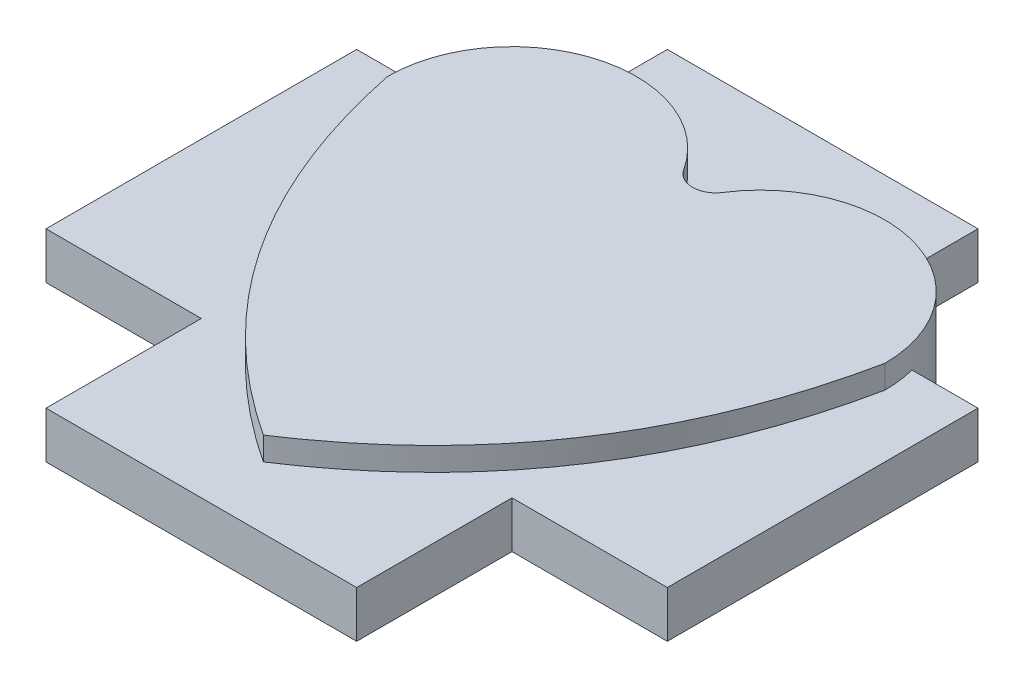
SolidWorks part; units mm, degrees
ref_plane "Front Plane" through (0, 0, 0) normal (0, 0, 1) x (1, 0, 0)
ref_plane "Top Plane" through (0, 0, 0) normal (0, 1, 0) x (1, 0, 0)
ref_plane "Right Plane" through (0, 0, 0) normal (1, 0, 0) x (0, 0, -1)
sketch "Sketch1" plane through (0, 0, 0) normal (0, 1, 0) x (1, 0, 0)
  line L0 (0, 8) -> (0, 4) construction
  line L1 (10, -10) -> (-10, -10)
  line L2 (10, -10) -> (10, 10)
  line L3 (10, 10) -> (-10, 10)
  line L4 (-10, -10) -> (-10, 10)
  line L5 (8, -8) -> (-8, -8) construction
  line L6 (8, -8) -> (8, 8) construction
  line L7 (8, 8) -> (-8, 8) construction
  line L8 (-8, -8) -> (-8, 8) construction
  line L9 (0, 4) -> (4, 4) construction
  line L10 (0, 4) -> (-4, 4) construction
  line L11 (0, -8) -> (0, -4.5) construction
  line L12 (0, -4.5) -> (-4, -4.5) construction
  line L13 (0, -4.5) -> (4, -4.5) construction
  arc A0 (-0.6316, 6.1573) -> (-8, 4) centre (-4, 4) ccw
  arc A1 (8, 4) -> (0.6316, 6.1573) centre (4, 4) ccw
  arc A2 (-0.6316, 6.1573) -> (0.6316, 6.1573) centre (0, 6.5617) ccw
  spline S0 degree 2 poles (-8, 4) (-6.4033, -3.8115) (0, -8) knots 0 0 0 1 1 1
  spline S1 degree 2 poles (8, 4) (6.4033, -3.8115) (0, -8) knots 0 0 0 1 1 1
  point P0 (0, 0)
  point P6 (0, 0)
  dimension "D3" = 0.75
  dimension "D1" = 20
  dimension "D2" = 20
  dimension "D4" = 16
  dimension "D5" = 4
  dimension "D6" = 4
  dimension "D8" = 3.5
  dimension "D9" = 4
  dimension "D10" = 4
extrude "Boss-Extrude3" add sketch "Sketch1" along normal blind 3 contours S1 A1 A0 S0
ref_plane "Plane1" through (0, 1.5, 0) normal (0, 1, 0) x (1, 0, 0)
sketch "Sketch2" plane through (0, 1.5, 0) normal (0, 1, 0) x (1, 0, 0)
  line L0 (-1.5, 5) -> (-1.5, -5)
  line L1 (8, -8) -> (-8, -8) construction
  line L2 (8, -8) -> (8, 8) construction
  line L3 (8, 8) -> (-8, 8) construction
  line L4 (-8, -8) -> (-8, 8) construction
  line L5 (0, 8) -> (0, -8) construction
  line L6 (8, 0) -> (-8, 0) construction
  line L7 (10, -10) -> (-10, -10) construction
  line L8 (10, -10) -> (10, 10) construction
  line L9 (10, 10) -> (-10, 10) construction
  line L10 (-10, -10) -> (-10, 10) construction
  line L11 (0, 10) -> (0, -10) construction
  line L12 (10, 0) -> (-10, 0) construction
  line L13 (-10, 5) -> (-1.5, 5)
  line L14 (-10, 5) -> (-10, -5)
  line L15 (-10, -5) -> (-1.5, -5)
  line L16 (10, 5) -> (10, -5)
  line L17 (0, -5) -> (0, 5) construction
  line L18 (-10, 0) -> (10, 0) construction
  line L19 (1.5, 5) -> (1.5, -5)
  line L20 (1.5, -5) -> (10, -5)
  line L21 (1.5, 5) -> (10, 5)
  line L23 (-5, 10) -> (5, 10)
  line L24 (-5, 10) -> (-5, -10)
  line L25 (-5, -10) -> (5, -10)
  line L26 (5, 10) -> (5, -10)
  line L27 (0, -10) -> (0, 10) construction
  line L28 (-5, 0) -> (5, 0) construction
  arc A2 (8, 4) -> (0.6316, 6.1573) centre (4, 4) ccw
  arc A3 (-0.6316, 6.1573) -> (-8, 4) centre (-4, 4) ccw
  arc A4 (8, 4) -> (0.6316, 6.1573) centre (4, 4) ccw
  arc A5 (-0.6316, 6.1573) -> (-8, 4) centre (-4, 4) ccw
  arc A7 (-0.6316, 6.1573) -> (0.6316, 6.1573) centre (0, 6.5617) ccw
  arc A8 (-0.6316, 6.1573) -> (0.6316, 6.1573) centre (0, 6.5617) ccw
  parabola Q2 (0, -8) -> (8, 4) focus (-2.2517, 1.4623) apex (4.6239, -3.7203)
  parabola Q3 (-8, 4) -> (0, -8) focus (2.2517, 1.4623) apex (-4.6239, -3.7203)
  parabola Q4 (0, -8) -> (8, 4) focus (-2.2517, 1.4623) apex (4.6239, -3.7203)
  parabola Q5 (-8, 4) -> (0, -8) focus (2.2517, 1.4623) apex (-4.6239, -3.7203)
  point P2 (0, 0)
  point P12 (0, 0)
  point P22 (0, 0)
  point P30 (0, 0)
  dimension "D7" = 1.5
  dimension "D2" = 16
  dimension "D3" = 16
  dimension "D4" = 20
  dimension "D5" = 20
  dimension "D6" = 10
  dimension "D8" = 1.5
  dimension "D9" = 10
  dimension "D1" = 0
extrude "Boss-Extrude4" add sketch "Sketch2" along normal blind 0.75 and the other way blind 0.75 contours Q5 A5 L13 L14 L15 L24 | Q5 L24 L15 | Q4 L26 L20 L16 L21 A4 | Q4 L20 L26 | A5 A4 L26 L23 L24 | Q5 L15 L24 L25 L26 L20 Q4
